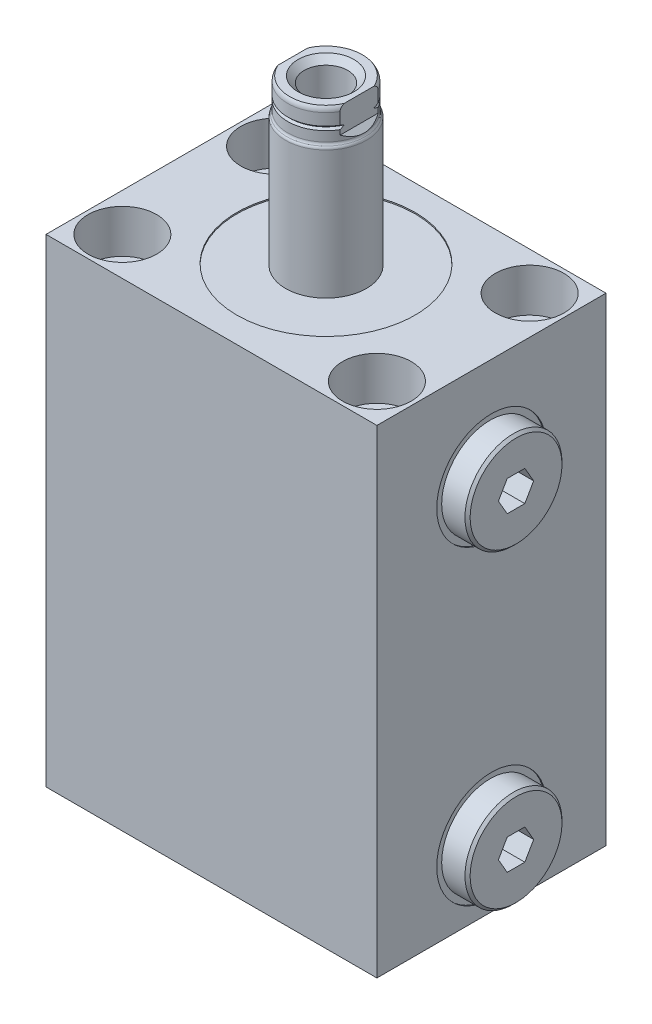
SolidWorks part; units mm, degrees
material "Alloy Steel"
ref_plane "Front Plane" through (0, 0, 0) normal (0, 0, 1) x (1, 0, 0)
ref_plane "Top Plane" through (0, 0, 0) normal (0, 1, 0) x (1, 0, 0)
ref_plane "Right Plane" through (0, 0, 0) normal (1, 0, 0) x (0, 0, -1)
sketch "Sketch1" plane through (0, 0, 0) normal (0, 1, 0) x (1, 0, 0)
  line L0 (-32.5, 22.5) -> (32.5, -22.5) construction
  line L1 (-32.5, 22.5) -> (32.5, 22.5)
  line L2 (-32.5, 22.5) -> (-32.5, -22.5)
  line L3 (-32.5, -22.5) -> (32.5, -22.5)
  line L4 (32.5, 22.5) -> (32.5, -22.5)
  point P4 (0, 0)
  dimension "D1" = 65
  dimension "D2" = 45
extrude "Extrude1" add sketch "Sketch1" along normal blind 94
sketch "Sketch2" plane through (0, 94, 0) normal (0, 1, 0) x (1, 0, 0)
  circle A0 centre (0, 0) radius 17.5
  dimension "D1" = 35
extrude "Cut-Extrude1" cut sketch "Sketch2" against normal blind 0.254
sketch "Sketch3" plane through (0, 0, 0) normal (0, 0, 1) x (1, 0, 0)
  line L0 (-6.848, 74) -> (35.4055, 74) construction
  line L1 (-32.5, 0) -> (32.5, 0) construction
  line L2 (32.5, 74) -> (32.5, 63.256)
  line L3 (32.5, 94) -> (32.5, 0) construction
  line L4 (32.5, 63.256) -> (32.246, 63.256)
  line L5 (32.246, 63.256) -> (32.246, 67.3452)
  line L6 (32.246, 67.3452) -> (31.5348, 68.0564)
  line L7 (31.5348, 68.0564) -> (16.752, 68.0564)
  line L8 (16.752, 68.0564) -> (16.752, 74)
  line L9 (16.752, 74) -> (32.5, 74)
  dimension "D1" = 74
  dimension "D2" = 21.488
  dimension "D3" = 0.254
  dimension "D4" = 11.8872
  dimension "D5" = 15.748
  dimension "D6" = 45
  dimension "D7" = 0.7112
revolve "Cut-Revolve1" cut sketch "Sketch3" angle 360 about L0
sketch "Sketch4" plane through (0, 0, 0) normal (0, 0, 1) x (1, 0, 0)
  line L0 (20.308, 74) -> (20.308, 79.9182)
  line L1 (31.5348, 74) -> (16.752, 74) construction
  line L2 (20.308, 79.9182) -> (32.246, 79.9182)
  line L3 (32.246, 79.9182) -> (32.246, 83.525)
  line L4 (32.246, 83.525) -> (37.326, 83.525)
  line L5 (37.326, 83.525) -> (37.326, 74)
  line L6 (37.326, 74) -> (20.308, 74)
  line L8 (32.246, 63.256) -> (32.246, 84.744) construction
  line L9 (8.7326, 74) -> (38.9701, 74) construction
  dimension "D1" = 11.938
  dimension "D2" = 11.8364
  dimension "D3" = 5.08
  dimension "D4" = 19.05
revolve "Revolve1" add sketch "Sketch4" angle 360 about L9
chamfer "Chamfer1" distance 0.508 angle 45 1 edges at (37.326, 74, 9.525)
sketch "Sketch5" plane through (37.326, 0, 0) normal (1, 0, 0) x (0, 0, -1)
  line L1 (1.7304, 76.9972) -> (-1.7304, 76.9972)
  line L2 (-1.7304, 76.9972) -> (-3.4609, 74)
  line L3 (-3.4609, 74) -> (-1.7304, 71.0028)
  line L4 (-1.7304, 71.0028) -> (1.7304, 71.0028)
  line L5 (1.7304, 71.0028) -> (3.4609, 74)
  line L6 (3.4609, 74) -> (1.7304, 76.9972)
  circle A0 centre (0, 74) radius 2.9972 construction
  dimension "D1" = 5.9944
extrude "Cut-Extrude2" cut sketch "Sketch5" against normal blind 5.9944
pattern_linear "LPattern1" count 2 spacing 61 along (0, -1, 0) of "Cut-Revolve1", "Revolve1", "Chamfer1", "Cut-Extrude2"
sketch "Sketch6" plane through (0, 0, 0) normal (0, 0, 1) x (1, 0, 0)
  line L0 (-32.5, 0) -> (32.5, 0) construction
  line L1 (0, 0) -> (0, 18.7888) construction
  line L12 (0, 0) -> (0, 14.8958)
  line L13 (5.7025, 0) -> (0, 0)
  line L14 (1.2446, 14.148) -> (0, 14.8958)
  line L15 (1.2446, 4.9529) -> (1.2446, 14.148)
  line L16 (1.7525, 4.445) -> (1.2446, 4.9529)
  line L17 (3.2512, 4.445) -> (1.7525, 4.445)
  line L18 (3.2512, 1.448) -> (3.2512, 4.445)
  line L19 (5.7025, 1.448) -> (3.2512, 1.448)
  line L20 (5.7025, 0) -> (5.7025, 1.448)
  dimension "D1" = 59
  dimension "D2" = 14.8958
  dimension "D3" = 2.4892
  dimension "D4" = 11.405
  dimension "D5" = 1.448
  dimension "D6" = 6.5024
  dimension "D7" = 4.445
  dimension "D8" = 45
  dimension "D9" = 0.5079
revolve "Cut-Revolve2" cut sketch "Sketch6" angle 360 about L1
sketch "Sketch7" plane through (0, 0, 0) normal (0, 0, 1) x (1, 0, 0)
  line L0 (0, 0) -> (0, 17.946) construction
  line L1 (0, 14.148) -> (0, 14.8958) construction
  line L2 (-32.5, 0) -> (32.5, 0) construction
  circle A0 centre (4.814, 0.5844) radius 0.889
  dimension "D1" = 9.628
  dimension "D2" = 1.778
  dimension "D3" = 0.5844
revolve "Revolve3" add sketch "Sketch7" angle 360 about L0
pattern_linear "LPattern2" count 2 spacing 25 along (-1, 0, 0) of "Cut-Revolve2", "Revolve3"
sketch "Sketch8" plane through (0, 0, 0) normal (0, 0, 1) x (1, 0, 0)
  line L0 (7.925, 93.746) -> (7.925, 118.9442)
  line L1 (7.1341, 126) -> (0, 126)
  line L2 (0, 126) -> (0, 93.746)
  line L3 (7.5, 125.0094) -> (7.5, 120)
  line L4 (7.925, 93.746) -> (0, 93.746)
  line L5 (0, 0) -> (0, 83.6966) construction
  line L6 (17.5, 93.746) -> (-17.5, 93.746) construction
  line L7 (-32.5, 0) -> (32.5, 0) construction
  arc A0 (7.5, 125.0094) -> (7.1341, 126) centre (5.976, 125.0094) ccw
  arc A1 (7.5, 120) -> (7.7125, 119.4721) centre (8.262, 120) ccw
  arc A2 (7.925, 118.9442) -> (7.7125, 119.4721) centre (7.163, 118.9442) ccw
  dimension "D1" = 1.524
  dimension "D7" = 0.762
  dimension "D8" = 0.762
  dimension "D2" = 6
  dimension "D3" = 126
  dimension "D4" = 0.9906
  dimension "D5" = 15
  dimension "D6" = 15.85
revolve "Revolve4" add sketch "Sketch8" angle 360 about L5
sketch "Sketch10" plane through (0, 0, 0) normal (0, 0, 1) x (1, 0, 0)
  line L0 (5.5, 126) -> (4.267, 124.767)
  line L1 (4.267, 124.767) -> (4.267, 105.68)
  line L2 (4.267, 105.68) -> (0, 103.1161)
  line L3 (0, 103.1161) -> (0, 126)
  line L4 (0, 126) -> (5.5, 126)
  line L5 (0, 126) -> (0, 82.7828) construction
  line L6 (7.1341, 126) -> (-7.1341, 126) construction
  dimension "D1" = 45
  dimension "D2" = 1.233
  dimension "D3" = 8.534
  dimension "D4" = 59
  dimension "D5" = 20.32
revolve "Cut-Revolve3" cut sketch "Sketch10" angle 360 about L5
sketch "Sketch11" plane through (0, 0, 0) normal (0, 0, 1) x (1, 0, 0)
  line L0 (7.5, 122.698) -> (7.119, 122.317)
  line L1 (7.119, 122.317) -> (7.5, 121.936)
  line L2 (7.5, 121.936) -> (7.5, 122.698)
  line L3 (7.5, 120) -> (7.5, 125.0094) construction
  line L4 (7.119, 122.317) -> (7.5, 122.317) construction
  line L5 (7.1341, 126) -> (-7.1341, 126) construction
  line L6 (0, 0) -> (0, 94.5745) construction
  dimension "D1" = 0.762
  dimension "D2" = 3.683
  dimension "D3" = 90
revolve "Cut-Revolve4" cut sketch "Sketch11" angle 360 about L6
sketch "Sketch12" plane through (0, 0, 0) normal (0, 0, 1) x (1, 0, 0)
  line L0 (0, 0) -> (0, 87.4273) construction
  line L1 (6.5, 126) -> (6.5, 121)
  line L2 (5.5, 126) -> (-5.5, 126) construction
  line L3 (6.5, 121) -> (7.925, 119.575)
  line L4 (7.925, 119.575) -> (7.925, 126)
  line L5 (7.925, 126) -> (6.5, 126)
  line L6 (7.925, 93.746) -> (7.925, 118.9442) construction
  line L7 (-7.925, 126) -> (-6.5, 126)
  line L8 (-7.925, 119.575) -> (-7.925, 126)
  line L9 (-6.5, 121) -> (-7.925, 119.575)
  line L10 (-6.5, 126) -> (-6.5, 121)
  dimension "D1" = 13
  dimension "D2" = 45
  dimension "D3" = 5
extrude "Cut-Extrude3" cut sketch "Sketch12" against normal through all and the other way through all
hole_wizard "Hole1" positions "Sketch14" profile "Sketch13" legacy end condition through all
sketch "Sketch14" plane through (0, 94, 0) normal (0, 1, 0) x (-1, 0, 0)
  line L0 (0, 0) -> (0, 30.0241) construction
  line L1 (0, 0) -> (32.2854, 0) construction
  point P0 (25, 15)
  point P10 (25, -15)
  point P12 (-25, -15)
  point P13 (-25, 15)
  dimension "D1" = 30
  dimension "D2" = 50
sketch "Sketch13" plane through (-25, 94, 15) normal (1, 0, 0) x (0, 0, 1)
  line L0 (0, 0) -> (0, 94.3046)
  line L1 (0, 94.3046) -> (4.2545, 94.3046)
  line L2 (4.2545, 94.3046) -> (4.2545, 8.509)
  line L3 (4.2545, 8.509) -> (6.7435, 8.509)
  line L4 (6.7435, 8.509) -> (6.7435, 0)
  line L5 (6.7435, 0) -> (0, 0)
  line L6 (0, 110) -> (0, -10) construction
  dimension "Diameter" = 8.509
  dimension "Depth" = 94.3046
  dimension "C-Bore Diameter" = 13.487
  dimension "C-Bore Depth" = 8.509
